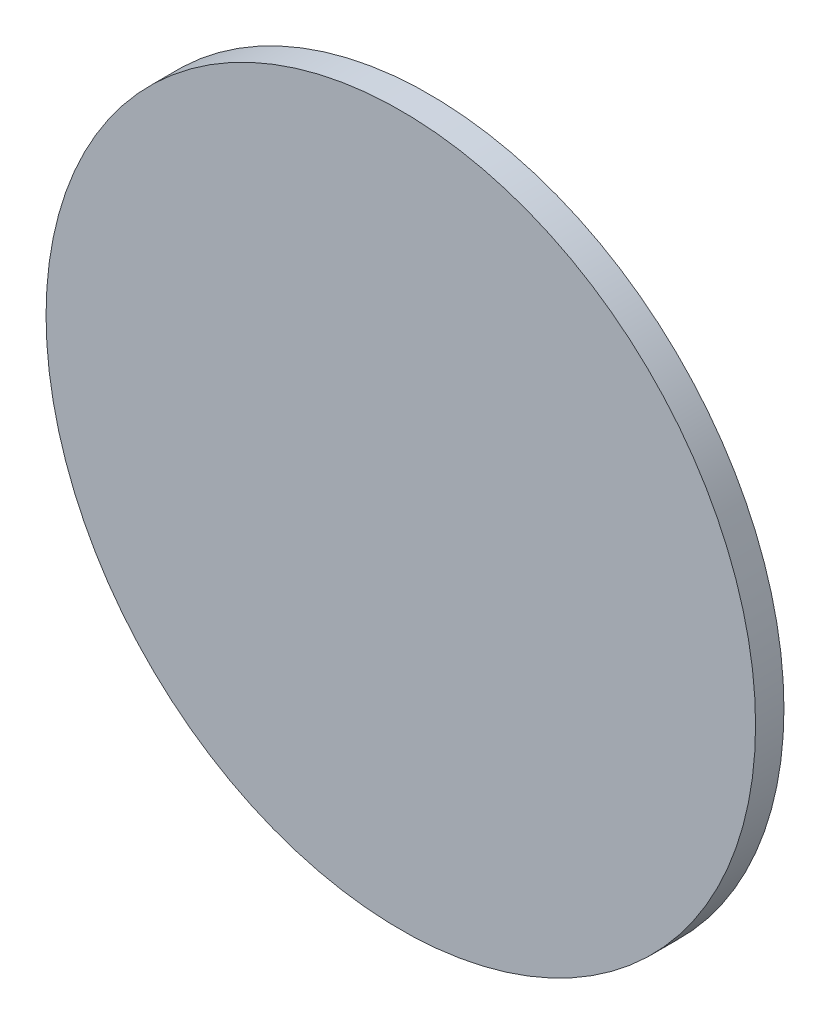
SolidWorks part; units mm, degrees
ref_plane "前视基准面" through (0, 0, 0) normal (0, 0, 1) x (1, 0, 0)
ref_plane "上视基准面" through (0, 0, 0) normal (0, 1, 0) x (1, 0, 0)
ref_plane "右视基准面" through (0, 0, 0) normal (1, 0, 0) x (0, 0, -1)
sketch "草图1" plane through (0, 0, 0) normal (0, 0, 1) x (1, 0, 0)
  circle A0 centre (0, 0) radius 12.5
  dimension "D1" = 25
extrude "凸台-拉伸1" add sketch "草图1" along normal blind 1 contours A0
